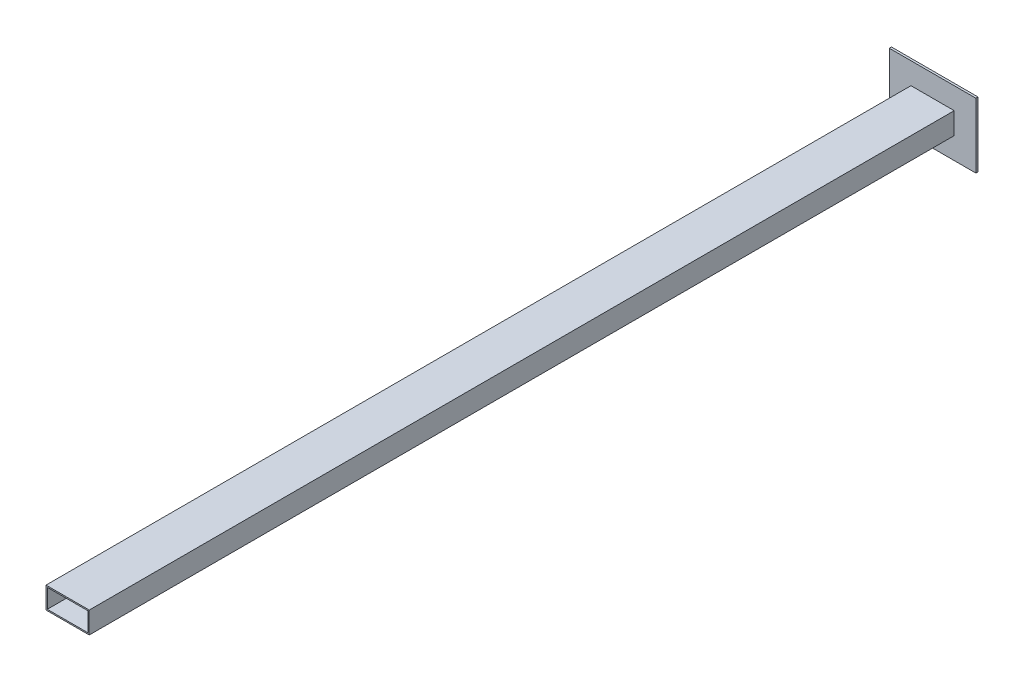
SolidWorks part; units mm, degrees
material "1.0570 (S355J2G3)"
ref_plane "Top Plane" through (0, 0, 0) normal (0, 0, 1) x (1, 0, 0)
ref_plane "Right Plane" through (0, 0, 0) normal (0, 1, 0) x (1, 0, 0)
ref_plane "Front Plane" through (0, 0, 0) normal (1, 0, 0) x (0, 0, -1)
sketch "Sketch1" plane through (0, 0, 0) normal (0, 0, 1) x (1, 0, 0)
  line L0 (3, 47) -> (97, 47)
  line L1 (0, 0) -> (100, 0)
  line L2 (0, 0) -> (0, 50)
  line L3 (0, 50) -> (100, 50)
  line L4 (100, 0) -> (100, 50)
  line L5 (97, 3) -> (97, 47)
  line L6 (3, 3) -> (97, 3)
  line L7 (3, 3) -> (3, 47)
  dimension "D1" = 100
  dimension "D2" = 50
  dimension "D3" = 3
extrude "Boss-Extrude1" add sketch "Sketch1" along normal blind 2000
sketch "Sketch2" plane through (0, 0, 0) normal (0, 0, -1) x (-1, 0, 0)
  line L0 (-100, 50) -> (0, 50) construction
  line L1 (-150, -50) -> (50, -50)
  line L2 (-150, -50) -> (-150, 100)
  line L3 (-150, 100) -> (50, 100)
  line L4 (50, -50) -> (50, 100)
  line L5 (-150, -50) -> (50, 100) construction
  line L6 (-150, 100) -> (50, -50) construction
  line L7 (0, 0) -> (-100, 0) construction
  line L8 (-100, 0) -> (-100, 50) construction
  line L9 (0, 50) -> (0, 0) construction
  point P0 (-50, 25)
  dimension "D1" = 50
  dimension "D2" = 50
  dimension "D3" = 50
  dimension "D4" = 50
extrude "Boss-Extrude2" add sketch "Sketch2" along normal blind 5
sketch "Sketch3" plane through (0, 0, 0) normal (0, -1, 0) x (1, 0, 0)
  line L0 (-60.2638, 0) -> (177.1148, 0)
  line L1 (150, 0) -> (-50, 0) construction
split "Split2" trim tools "Sketch3" bodies to split 103 resulting bodies 106 107
other "Save Bodies1"
